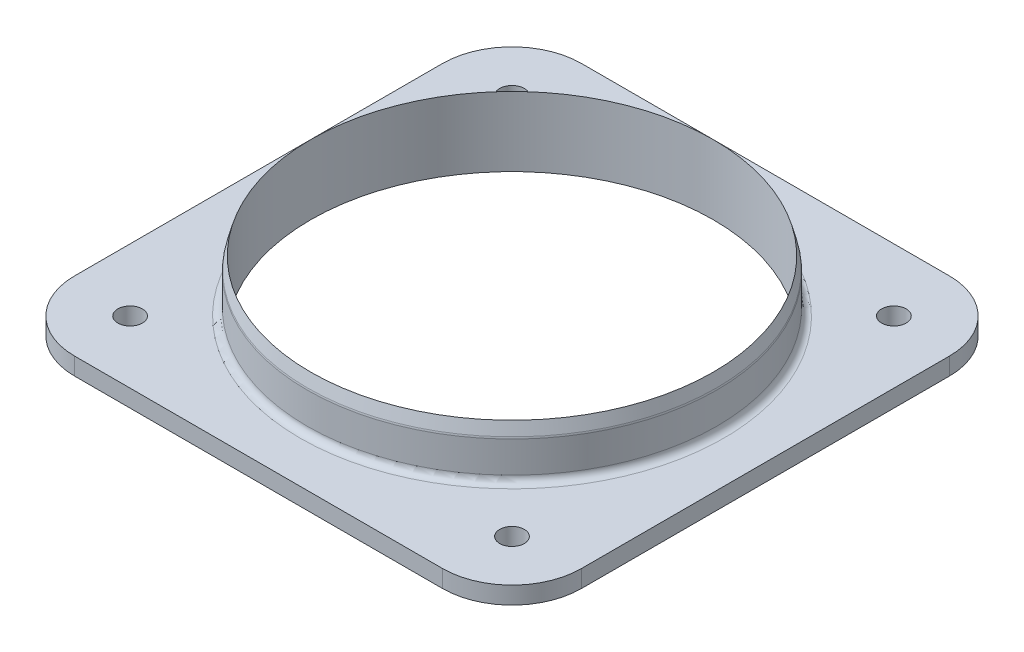
SolidWorks part; units mm, degrees
material "ABS"
ref_plane "Front Plane" through (0, 0, 0) normal (0, 0, 1) x (1, 0, 0)
ref_plane "Top Plane" through (0, 0, 0) normal (0, 1, 0) x (1, 0, 0)
ref_plane "Right Plane" through (0, 0, 0) normal (1, 0, 0) x (0, 0, -1)
sketch "Sketch1" plane through (0, 0, 0) normal (0, 1, 0) x (1, 0, 0)
  line L1 (46.355, -46.355) -> (-46.355, -46.355)
  line L2 (46.355, -46.355) -> (46.355, 46.355)
  line L3 (46.355, 46.355) -> (-46.355, 46.355)
  line L4 (-46.355, -46.355) -> (-46.355, 46.355)
  line L5 (46.355, -46.355) -> (-46.355, 46.355) construction
  line L6 (46.355, 46.355) -> (-46.355, -46.355) construction
  circle A0 centre (0, 0) radius 36.83
  point P0 (0, 0)
  dimension "D1" = 73.66
  dimension "D3" = 92.71
extrude "Boss-Extrude1" add sketch "Sketch1" along normal blind 3.175
sketch "Sketch2" plane through (0, 3.175, 0) normal (0, 1, 0) x (1, 0, 0)
  line L1 (34.925, -34.925) -> (-34.925, -34.925) construction
  line L2 (34.925, -34.925) -> (34.925, 34.925) construction
  line L3 (34.925, 34.925) -> (-34.925, 34.925) construction
  line L4 (-34.925, -34.925) -> (-34.925, 34.925) construction
  line L5 (34.925, -34.925) -> (-34.925, 34.925) construction
  line L6 (34.925, 34.925) -> (-34.925, -34.925) construction
  circle A0 centre (-34.925, 34.925) radius 2.25
  point P0 (0, 0)
  dimension "D2" = 4.5
  dimension "D1" = 69.85
extrude "Cut-Extrude1" cut sketch "Sketch2" against normal through all
pattern_circular "CirPattern1" count 4 over 360 about axis through (0, 0, 0) along (0, 1, 0) of "Cut-Extrude1"
fillet "Fillet1" radius 12.7 4 edges at (-46.355, 1.5875, -46.355) (-46.355, 1.5875, 46.355) (46.355, 1.5875, 46.355) (46.355, 1.5875, -46.355)
sketch "Sketch4" plane through (0, 0, 0) normal (0, 0, 1) x (1, 0, 0)
  line L1 (36.83, 3.175) -> (36.83, 12.7)
  line L2 (46.355, 3.175) -> (33.655, 3.175) construction
  line L3 (0, -1000) -> (0, 49000) construction
  line L4 (36.83, 12.7) -> (37.465, 10.3301)
  line L5 (37.465, 10.3301) -> (37.465, 3.175)
  line L6 (37.465, 3.175) -> (36.83, 3.175)
  dimension "D1" = 12.7
  dimension "D2" = 0.635
  dimension "D3" = 15
revolve "Revolve1" add sketch "Sketch4" angle 360 about L3
fillet "Fillet2" radius 1.27 2 edges at (37.465, 10.3301, 0) (37.465, 3.175, 0)
